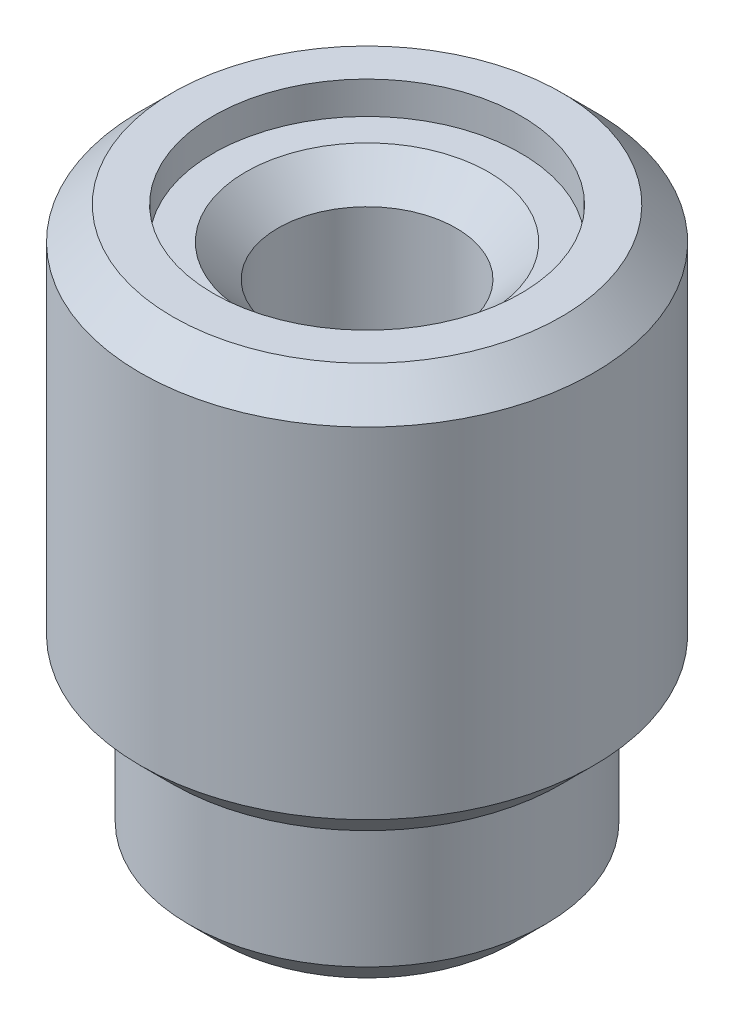
SolidWorks part; units mm, degrees
material "AISI 304"
ref_plane "Front Plane" through (0, 0, 0) normal (0, 0, 1) x (1, 0, 0)
ref_plane "Top Plane" through (0, 0, 0) normal (0, 1, 0) x (1, 0, 0)
ref_plane "Right Plane" through (0, 0, 0) normal (1, 0, 0) x (0, 0, -1)
sketch "Sketch1" plane through (0, 0, 0) normal (0, 1, 0) x (1, 0, 0)
  circle A0 centre (0, 0) radius 2.794
  dimension "D1" = 5.588
extrude "Boss-Extrude1" add sketch "Sketch1" along normal blind 2.54
sketch "Sketch2" plane through (0, 2.54, 0) normal (0, 1, 0) x (1, 0, 0)
  circle A0 centre (0, 0) radius 3.556
extrude "Boss-Extrude2" add sketch "Sketch2" along normal blind 6.35
sketch "Sketch3" plane through (0, 8.89, 0) normal (0, 1, 0) x (1, 0, 0)
  circle A0 centre (0, 0) radius 1.397
extrude "Cut-Extrude1" cut sketch "Sketch3" against normal through all
sketch "Sketch4" plane through (0, 8.89, 0) normal (0, 1, 0) x (1, 0, 0)
  circle A0 centre (0, 0) radius 2.413
extrude "Cut-Extrude2" cut sketch "Sketch4" against normal blind 0.508
sketch "Sketch5" plane through (0, 0, 0) normal (0, -1, 0) x (1, 0, 0)
  circle A0 centre (0, 0) radius 1.9939
  dimension "D1" = 3.9878
extrude "Cut-Extrude3" cut sketch "Sketch5" against normal blind 5.08
chamfer "Chamfer1" distance 0.508 angle 45 3 edges at (0, 2.54, 3.556) (0, 8.89, 3.556) (0, 0, 2.794)
chamfer "Chamfer2" distance 0.254 angle 45 1 edges at (0, 0, -1.9939)
chamfer "Chamfer3" distance 0.508 angle 45 1 edges at (0, 8.382, 1.397)
